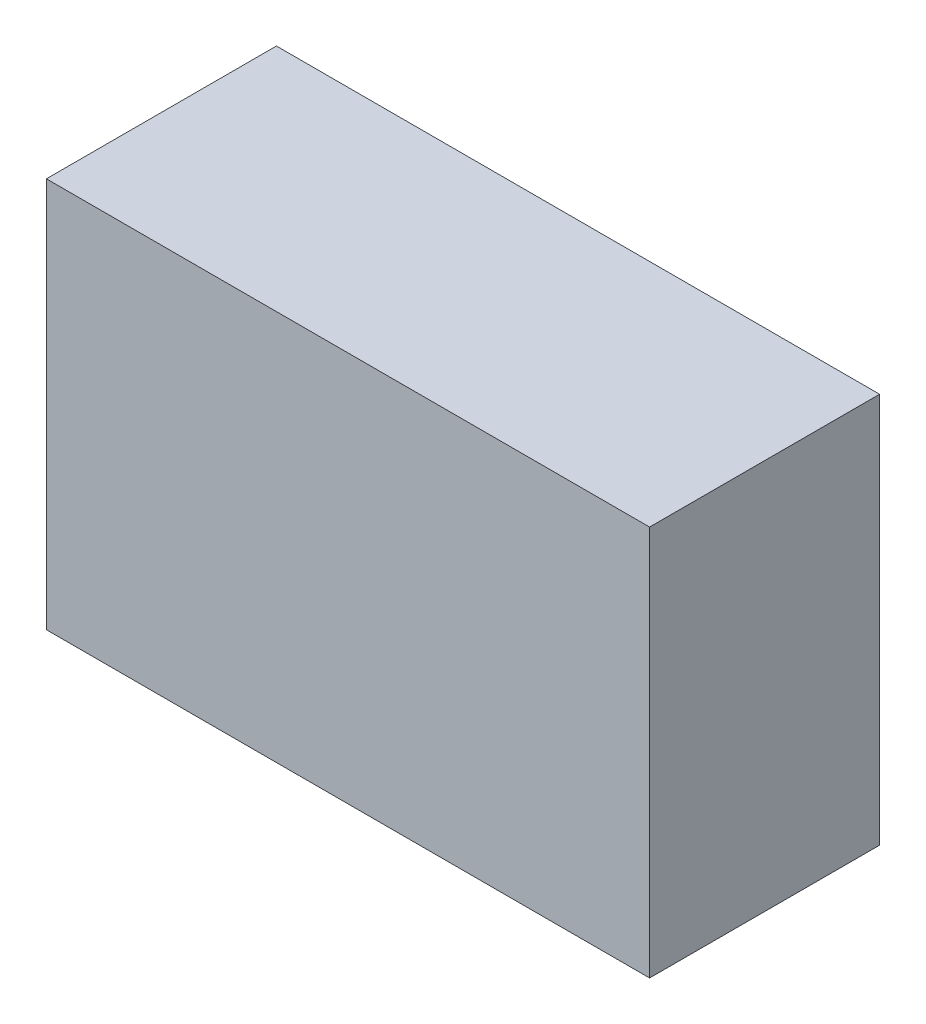
SolidWorks part; units mm, degrees
ref_plane "Front Plane" through (0, 0, 0) normal (0, 0, 1) x (1, 0, 0)
ref_plane "Top Plane" through (0, 0, 0) normal (0, 1, 0) x (1, 0, 0)
ref_plane "Right Plane" through (0, 0, 0) normal (1, 0, 0) x (0, 0, -1)
sketch "Sketch1" plane through (0, 0, 0) normal (0, 0, 1) x (1, 0, 0)
  line L1 (-74.8395, -13.1269) -> (43.1605, -13.1269)
  line L2 (-74.8395, -13.1269) -> (-74.8395, 63.2731)
  line L3 (-74.8395, 63.2731) -> (43.1605, 63.2731)
  line L4 (43.1605, -13.1269) -> (43.1605, 63.2731)
  line L5 (-74.8395, -13.1269) -> (43.1605, 63.2731) construction
  line L6 (-74.8395, 63.2731) -> (43.1605, -13.1269) construction
  point P0 (0, 0)
  dimension "D1" = 118
  dimension "D2" = 76.4
extrude "Boss-Extrude1" add sketch "Sketch1" against normal blind 45
